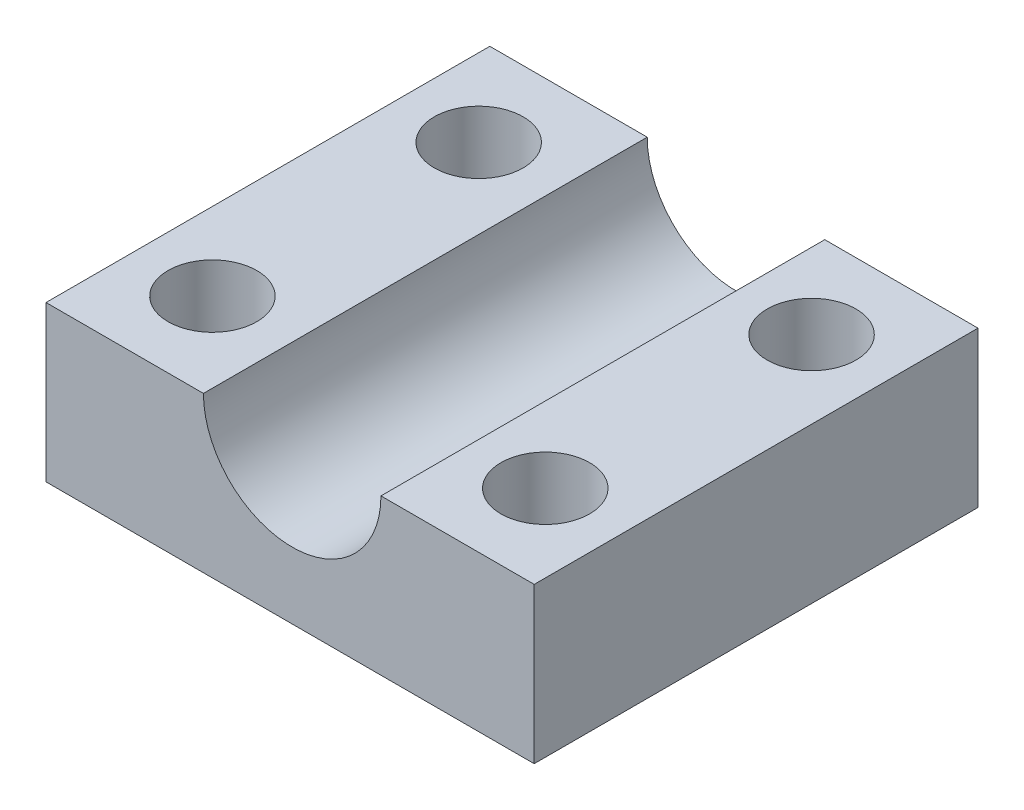
SolidWorks part; units mm, degrees
material "Ductile Iron (SN)"
ref_plane "Front Plane" through (0, 0, 0) normal (0, 0, 1) x (1, 0, 0)
ref_plane "Top Plane" through (0, 0, 0) normal (0, 1, 0) x (1, 0, 0)
ref_plane "Right Plane" through (0, 0, 0) normal (1, 0, 0) x (0, 0, -1)
sketch "Sketch1" plane through (0, 0, 0) normal (0, 1, 0) x (1, 0, 0)
  line L1 (-22.1889, 23.5576) -> (21.8111, 23.5576)
  line L2 (-22.1889, 23.5576) -> (-22.1889, -16.4424)
  line L3 (-22.1889, -16.4424) -> (21.8111, -16.4424)
  line L4 (21.8111, 23.5576) -> (21.8111, -16.4424)
  circle A0 centre (14.8111, -8.4424) radius 4
  circle A1 centre (14.8111, 15.5576) radius 4
  circle A2 centre (-15.1889, 15.5576) radius 4
  circle A3 centre (-15.1889, -8.4424) radius 4
  point P0 (0, 0)
  dimension "D3" = 7
  dimension "D4" = 8
  dimension "D5" = 7
  dimension "D1" = 40
  dimension "D2" = 44
  dimension "D6" = 8
  dimension "D7" = 8
extrude "Boss-Extrude1" add sketch "Sketch1" along normal blind 14
sketch "Sketch2" plane through (0, 0, 0) normal (0, 0, 1) x (1, 0, 0)
  line L0 (-22.1889, 14) -> (21.8111, 14) construction
  circle A0 centre (0, 14) radius 8
  dimension "D2" = 0
  dimension "D1" = 16
extrude "Cut-Extrude1" cut sketch "Sketch2" along normal up to surface and the other way up to surface up to face at (-0.1889, 7, 16.4424) other way up to face at (-0.1889, 7, -23.5576)
